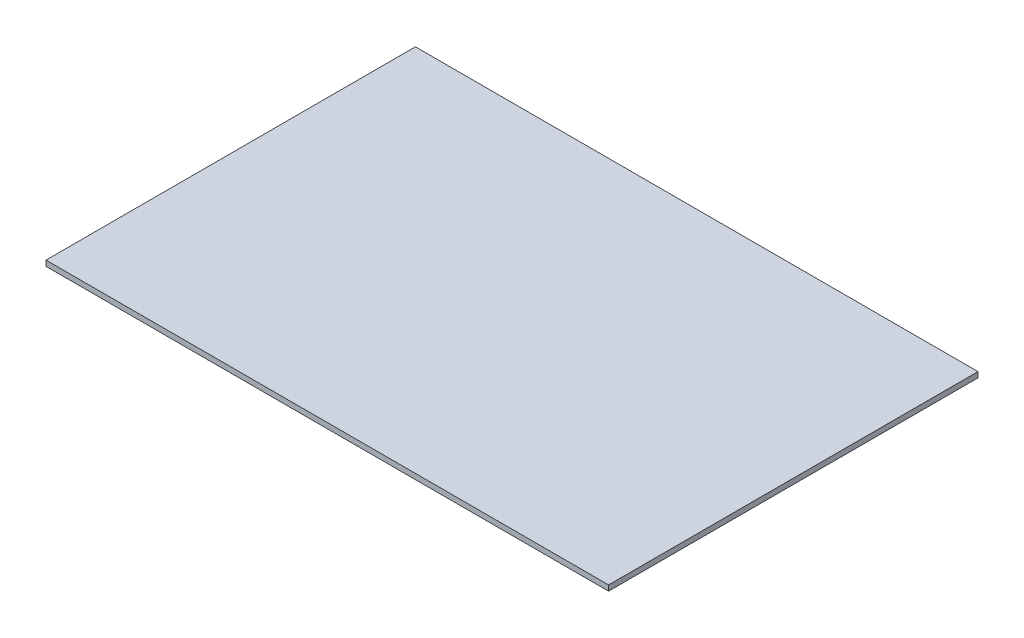
SolidWorks part; units mm, degrees
ref_plane "Front Plane" through (0, 0, 0) normal (0, 0, 1) x (1, 0, 0)
ref_plane "Top Plane" through (0, 0, 0) normal (0, 1, 0) x (1, 0, 0)
ref_plane "Right Plane" through (0, 0, 0) normal (1, 0, 0) x (0, 0, -1)
sketch "Sketch1" plane through (0, 0, 0) normal (0, 1, 0) x (1, 0, 0)
  line L1 (-150, -98.5) -> (150, -98.5)
  line L2 (-150, -98.5) -> (-150, 98.5)
  line L3 (-150, 98.5) -> (150, 98.5)
  line L4 (150, -98.5) -> (150, 98.5)
  line L5 (-150, -98.5) -> (150, 98.5) construction
  line L6 (-150, 98.5) -> (150, -98.5) construction
  point P0 (0, 0)
  dimension "D1" = 300
  dimension "D2" = 197
extrude "Boss-Extrude1" add sketch "Sketch1" along normal blind 2.9
